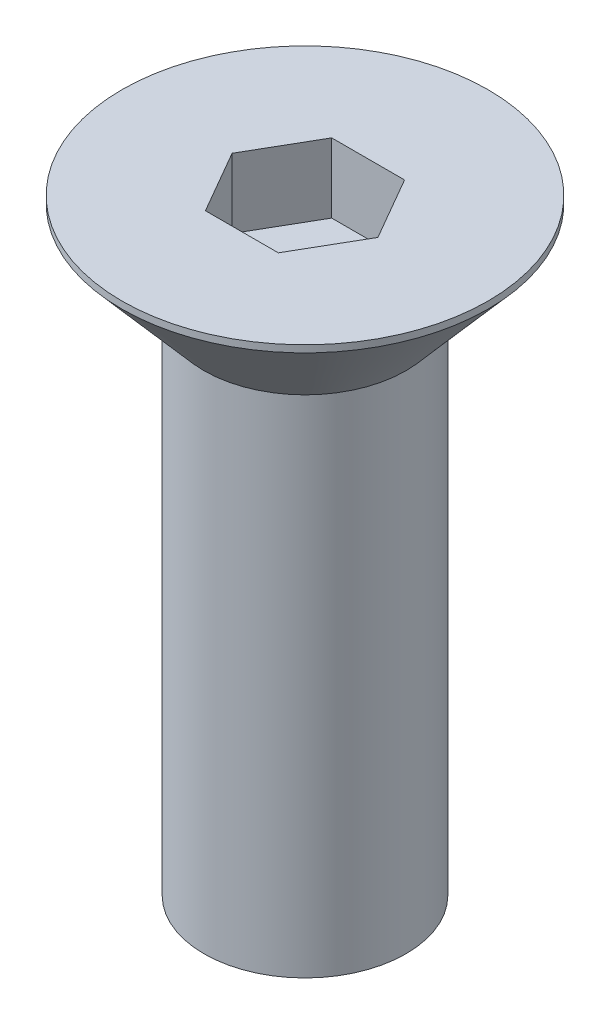
SolidWorks part; units mm, degrees
ref_plane "Front" through (0, 0, 0) normal (0, 0, 1) x (1, 0, 0)
ref_plane "Top" through (0, 0, 0) normal (0, 1, 0) x (1, 0, 0)
ref_plane "Side" through (0, 0, 0) normal (1, 0, 0) x (0, 0, -1)
sketch "Sketch1" plane through (0, 0, 0) normal (0, 0, 1) x (1, 0, 0)
  line L0 (0, -1.8236) -> (0, 5.741) construction
  line L1 (0, 6.3754) -> (11.5094, 6.3754)
  line L2 (11.5094, 6.3754) -> (11.5094, 5.9352)
  line L3 (11.5094, 5.9352) -> (6.35, 0)
  line L4 (6.35, 0) -> (0, 0)
  line L5 (0, 0) -> (0, 6.3754)
  line L6 (-11.5094, 5.9352) -> (-6.35, 0) construction
  dimension "HeadDia" = 23.0188
  dimension "D2" = 82
  dimension "BodyDia" = 12.7
  dimension "HeadHeight" = 6.3754
revolve "Head" add sketch "Sketch1" angle 360 about L0
sketch "Sketch2" plane through (0, 0, 0) normal (0, 1, 0) x (1, 0, 0)
  circle A0 centre (0, 0) radius 6.35 construction
  circle A1 centre (0, 0) radius 6.35
extrude "Length" add sketch "Sketch2" against normal blind 31.75
sketch "Sketch3" plane through (0, 6.3754, 0) normal (0, 1, 0) x (-1, 0, 0)
  line L1 (2.2914, 3.9688) -> (-2.2914, 3.9688)
  line L2 (-2.2914, 3.9688) -> (-4.5827, 0)
  line L3 (-4.5827, 0) -> (-2.2914, -3.9688)
  line L4 (-2.2914, -3.9688) -> (2.2914, -3.9688)
  line L5 (2.2914, -3.9688) -> (4.5827, 0)
  line L6 (4.5827, 0) -> (2.2914, 3.9688)
  circle A1 centre (0, 0) radius 3.9688 construction
  dimension "SocketSize" = 7.9375
extrude "Cut-Extrude1" cut sketch "Sketch3" against normal blind 4.3688
